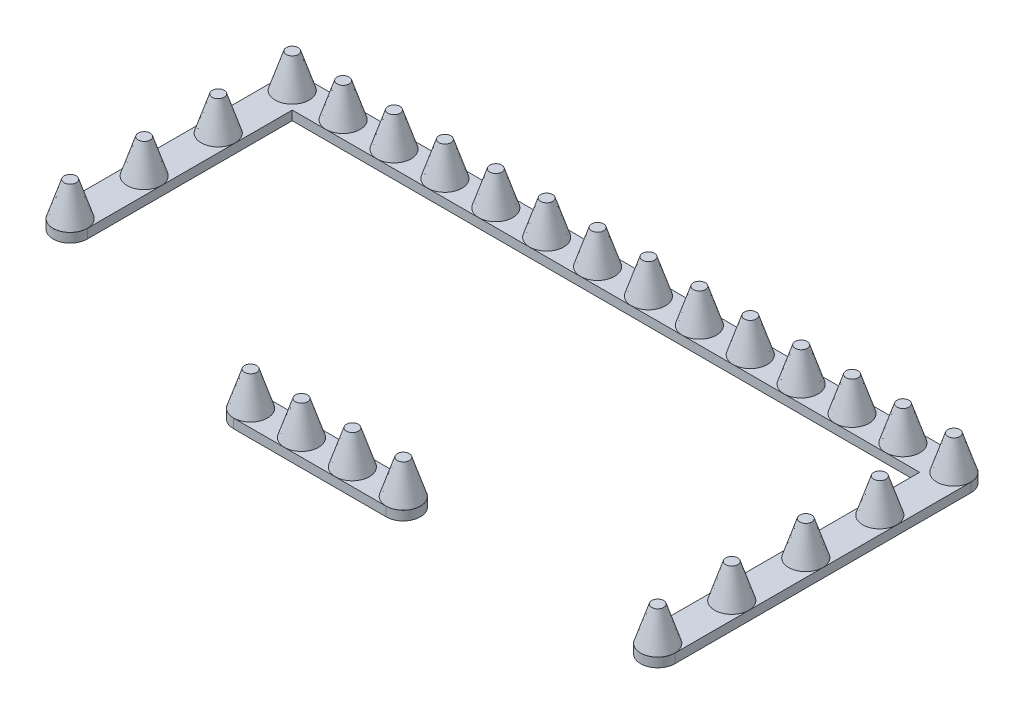
SolidWorks part; units mm, degrees
ref_plane "前视基准面" through (0, 0, 0) normal (0, 0, 1) x (1, 0, 0)
ref_plane "上视基准面" through (0, 0, 0) normal (0, 1, 0) x (1, 0, 0)
ref_plane "右视基准面" through (0, 0, 0) normal (1, 0, 0) x (0, 0, -1)
sketch "草图2" plane through (0, 0, 0) normal (0, 0, 1) x (1, 0, 0)
  line L0 (0, -0.5453) -> (0, 73.4547)
  line L1 (0, 73.4547) -> (13, 73.4547)
  line L2 (13, 73.4547) -> (37, -0.5453)
  line L3 (37, -0.5453) -> (0, -0.5453)
  dimension "D1" = 37
  dimension "D2" = 74
  dimension "D3" = 13
revolve "旋转1" add sketch "草图2" angle 360 about L0
sketch "草图4" plane through (0, 0, 0) normal (0, 1, 0) x (1, 0, 0)
  line L0 (0, 0) -> (0, -63.2129) construction
  line L1 (0, -40.7) -> (0, 40.7) construction
  line L2 (0, 0) -> (94.6609, 0) construction
pattern_linear "阵列(线性)3" count 4 spacing 160 along (0, 0, 1) of bodies 107
pattern_linear "阵列(线性)4" count 14 spacing 110 along (1, 0, 0) of bodies 107
pattern_linear "阵列(线性)5" count 5 spacing 160 along (0, 0, 1) of bodies 125
pattern_linear "阵列(线性)6" count 2 spacing 550 along (-1, 0, 0) of bodies 129
pattern_linear "阵列(线性)7" count 4 spacing 110 along (-1, 0, 0) of bodies 130
sketch "草图5" plane through (0, 0, 0) normal (0, 1, 0) x (1, 0, 0)
  line L0 (0, 0) -> (1430, 0) construction
  line L1 (1430, 0) -> (1430, -640) construction
  line L2 (0, -480) -> (0, 0) construction
  line L3 (550, -640) -> (880, -640) construction
  line L4 (37, -480) -> (37, -37)
  line L5 (37, -37) -> (1393, -37)
  line L6 (1393, -37) -> (1393, -640)
  line L7 (-37, -480) -> (-37, 0)
  line L8 (0, 37) -> (1430, 37)
  line L9 (1467, 0) -> (1467, -640)
  line L10 (550, -677) -> (880, -677)
  line L11 (550, -603) -> (880, -603)
  line L12 (-37, 37) -> (1467, 37) construction
  line L13 (-37, -480) -> (-37, 37) construction
  line L14 (1467, 37) -> (1467, -640) construction
  circle A0 centre (550, -640) radius 37 construction
  circle A1 centre (880, -640) radius 37 construction
  circle A2 centre (1430, -640) radius 37 construction
  circle A3 centre (1430, 0) radius 37 construction
  circle A4 centre (0, -480) radius 37 construction
  circle A5 centre (0, 0) radius 37 construction
  circle A6 centre (550, -640) radius 37 construction
  circle A7 centre (880, -640) radius 37 construction
  circle A8 centre (1430, -640) radius 37 construction
  arc A9 (1467, 0) -> (1430, 37) centre (1430, 0) ccw
  circle A10 centre (0, -480) radius 37 construction
  arc A11 (0, 37) -> (-37, 0) centre (0, 0) ccw
  arc A12 (-37, -480) -> (37, -480) centre (0, -480) ccw
  arc A13 (1393, -640) -> (1467, -640) centre (1430, -640) ccw
  arc A14 (880, -603) -> (880, -677) centre (880, -640) cw
  arc A15 (550, -603) -> (550, -677) centre (550, -640) ccw
  dimension "D1" = 37
  dimension "D2" = 37
  dimension "D3" = 37
  dimension "D4" = 37
extrude "凸台-拉伸3" add sketch "草图5" against normal blind 20
